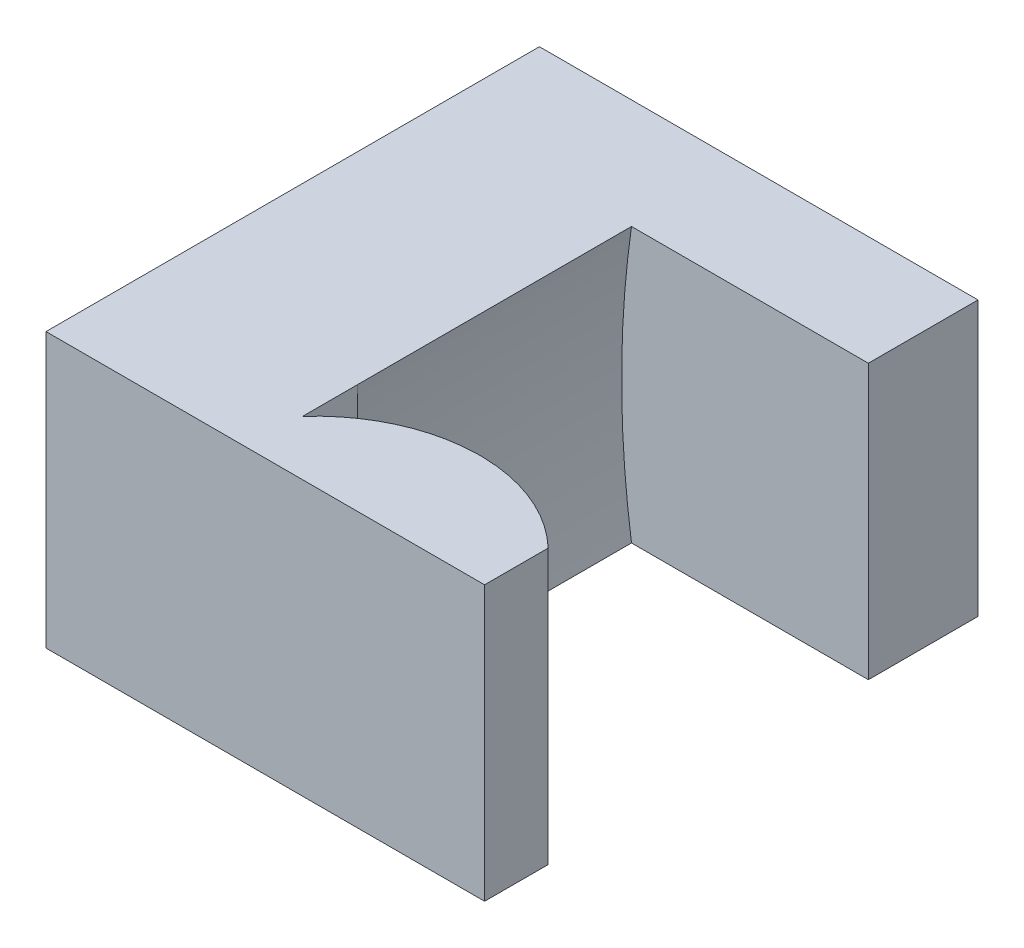
SolidWorks part; units mm, degrees
ref_plane "Front Plane" through (0, 0, 0) normal (0, 0, 1) x (1, 0, 0)
ref_plane "Top Plane" through (0, 0, 0) normal (0, 1, 0) x (1, 0, 0)
ref_plane "Right Plane" through (0, 0, 0) normal (1, 0, 0) x (0, 0, -1)
sketch "Sketch1" plane through (0, 0, 0) normal (0, 0, 1) x (1, 0, 0)
  line L1 (-13, 2.5) -> (-21, 2.5)
  line L2 (-13, 2.5) -> (-13, -2.5)
  line L3 (-13, -2.5) -> (-21, -2.5)
  line L4 (-21, 2.5) -> (-21, -2.5)
  point P4 (-13, 0)
  dimension "D1" = 13
  dimension "D2" = 5
  dimension "D3" = 8
extrude "Boss-Extrude1" add sketch "Sketch1" along normal blind 2
sketch "Sketch2" plane through (0, 0, 0) normal (0, 0, -1) x (-1, 0, 0)
  line L4 (13, 2.5) -> (13, -2.5)
  line L5 (13, -2.5) -> (21, -2.5)
  line L6 (21, -2.5) -> (21, 2.5)
  line L7 (21, 2.5) -> (13, 2.5)
  line L8 (13, 2.5) -> (13, -2.5)
  line L9 (13, -2.5) -> (21, -2.5)
  line L10 (21, -2.5) -> (21, 2.5)
  line L11 (21, 2.5) -> (13, 2.5)
  arc A0 (15.5571, -8.0142) -> (15.5571, 8.0142) centre (0, 0) ccw construction
  arc A1 (15.5571, -8.0142) -> (15.5571, 8.0142) centre (0, 0) ccw
  line M7 (21, -2.5) -> (21, 2.5)
  line M8 (21, 2.5) -> (13, 2.5)
  dimension "D1" = 0
extrude "Boss-Extrude2" add sketch "Sketch2" along normal up to surface (5 mm away) contours A1 L9 M7 M8
sketch "Sketch3" plane through (0, 0, -5) normal (0, 0, -1) x (-1, 0, 0)
  line L3 (13, -2.5) -> (17.3205, -2.5)
  line L4 (17.3205, 2.5) -> (13, 2.5)
  line L5 (13, 2.5) -> (13, -2.5)
  line L6 (13, -2.5) -> (17.3205, -2.5)
  line L7 (17.3205, 2.5) -> (13, 2.5)
  line L8 (13, 2.5) -> (13, -2.5)
  line L9 (17.3205, -2.5) -> (21, -2.5)
  line L10 (21, -2.5) -> (21, 2.5)
  line L11 (21, 2.5) -> (17.3205, 2.5)
  line L12 (17.3205, -2.5) -> (21, -2.5)
  line L13 (21, -2.5) -> (21, 2.5)
  line L14 (21, 2.5) -> (17.3205, 2.5)
  arc A1 (17.3205, -2.5) -> (17.3205, 2.5) centre (0, 0) ccw
  arc A2 (17.3205, -2.5) -> (17.3205, 2.5) centre (0, 0) ccw
  arc A3 (17.3205, -2.5) -> (17.3205, 2.5) centre (0, 0) ccw
  arc A4 (17.3205, -2.5) -> (17.3205, 2.5) centre (0, 0) ccw
  arc M5 (17.3205, 2.5) -> (17.3205, -2.5) centre (0, 0) cw
  line M6 (17.3205, -2.5) -> (21, -2.5)
  line M7 (21, -2.5) -> (21, 2.5)
  line M8 (21, 2.5) -> (17.3205, 2.5)
  dimension "D1" = 0
  dimension "D2" = 0
extrude "Boss-Extrude5" add sketch "Sketch3" along normal blind 2 contours M8 M5 M6 M7 | L7 L8 L6 M5
sketch "Sketch4" plane through (0, 2.5, 0) normal (0, 1, 0) x (1, 0, 0)
  line L0 (-15.1603, 0) -> (-17.3205, -1)
  line L1 (-13, 0) -> (-17.3205, 0) construction
  line L2 (-17.3205, -1) -> (-17.3205, 0)
  line L3 (-17.3205, 0) -> (-15.1603, 0)
  circle A0 centre (-15.0836, -2.999) radius 3
  point P9 (0, 0)
  point P10 (0, 0)
  line M3 (-13, 0) -> (-17.3205, 0)
  line M10 (-13, -2) -> (-13, 0)
  dimension "D2" = 6
  dimension "D1" = 1
extrude "Cut-Extrude2" cut sketch "Sketch4" against normal through all both and the other way through all contours A0 M10 M3 | A0 L2 M3
